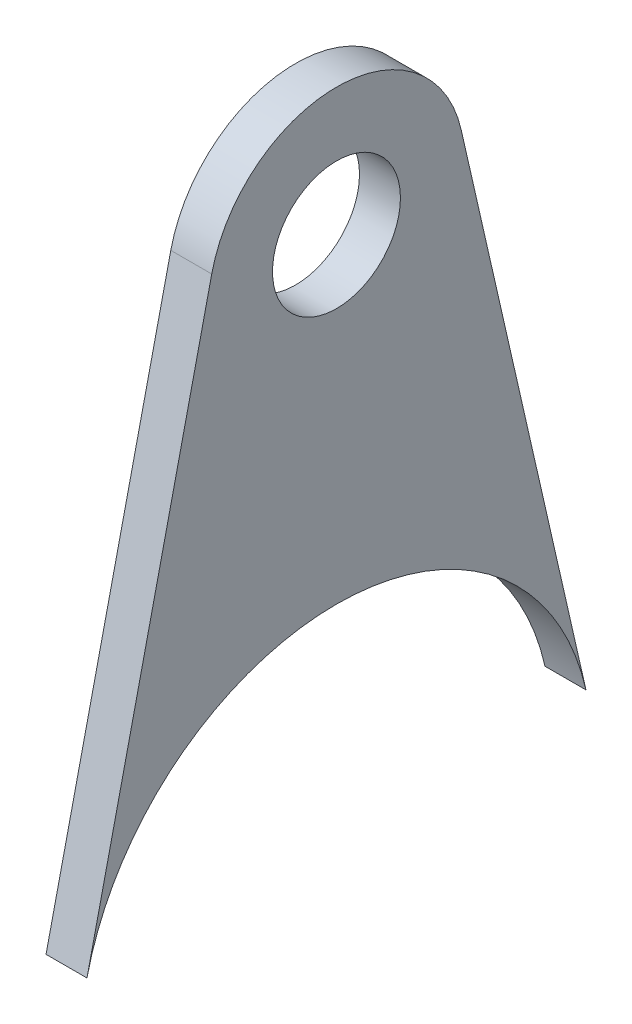
SolidWorks part; units mm, degrees
material "Plain Carbon Steel"
ref_plane "Front Plane" through (0, 0, 0) normal (0, 0, 1) x (1, 0, 0)
ref_plane "Top Plane" through (0, 0, 0) normal (0, 1, 0) x (1, 0, 0)
ref_plane "Right Plane" through (0, 0, 0) normal (1, 0, 0) x (0, 0, -1)
sketch "Sketch1" plane through (0, 0, 0) normal (1, 0, 0) x (0, 0, -1)
  line L0 (-12.3824, -9.8778) -> (-6.1912, 17.2861)
  line L2 (6.1912, 17.2861) -> (12.3824, -9.8778)
  arc A0 (12.3824, -9.8778) -> (-12.3824, -9.8778) centre (0, -12.7) ccw
  arc A1 (6.1912, 17.2861) -> (-6.1912, 17.2861) centre (0, 15.875) ccw
  point P9 (0, 0)
  dimension "D1" = 25.4
  dimension "D3" = 6.35
  dimension "D2" = 15.875
extrude "Boss-Extrude1" add sketch "Sketch1" along normal mid plane 2.032
sketch "Sketch2" plane through (1.016, 0, 0) normal (1, 0, 0) x (0, 0, -1)
  circle A0 centre (0, 15.875) radius 3.175
  arc A1 (6.1912, 17.2861) -> (-6.1912, 17.2861) centre (0, 15.875) ccw construction
  dimension "D1" = 6.35
extrude "Cut-Extrude1" cut sketch "Sketch2" against normal through all
